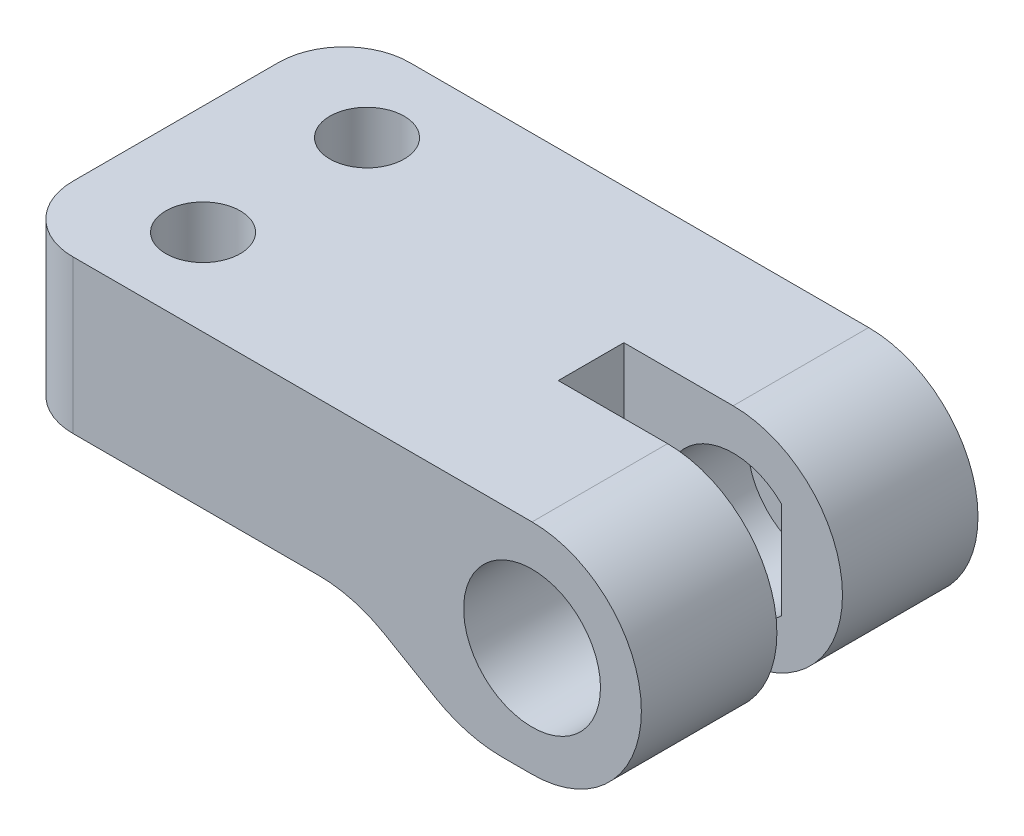
SolidWorks part; units mm, degrees
ref_plane "Płaszczyzna przednia" through (0, 0, 0) normal (0, 0, 1) x (1, 0, 0)
ref_plane "Płaszczyzna górna" through (0, 0, 0) normal (0, 1, 0) x (1, 0, 0)
ref_plane "Płaszczyzna prawa" through (0, 0, 0) normal (1, 0, 0) x (0, 0, -1)
sketch "Szkic1" plane through (0, 0, 0) normal (0, 0, 1) x (1, 0, 0)
  line L4 (0, 0) -> (-24, 0)
  line L5 (0, 0) -> (0, 10)
  line L6 (0, 10) -> (-24, 10)
  line L7 (-24, 0) -> (-24, 10)
  arc A0 (0, 10) -> (0, 0) centre (0, 5) cw
  dimension "D1" = 24
  dimension "D2" = 10
extrude "Dodanie-wyciągnięcie1" add sketch "Szkic1" along normal blind 15.4 contours A0 L5
sketch "Szkic2" plane through (0, 0, 15.4) normal (0, 0, 1) x (1, 0, 0)
  line L0 (0, 0) -> (-24, 0) construction
  circle A0 centre (0, 5) radius 3.13
  dimension "D1" = 5
  dimension "4" = 6.26
extrude "Wytnij-wyciągnięcie1" cut sketch "Szkic2" against normal blind 13
sketch "Szkic8" plane through (0, 4.76, 0) normal (0, 1, 0) x (1, 0, 0)
  circle A0 centre (-10, -9) radius 2
  dimension "D1" = 4
extrude "Wytnij-wyciągnięcie6" [suppressed] cut sketch "Szkic8" against normal through all
sketch "Szkic9" plane through (0, 0, 0) normal (0, 0, -1) x (-1, 0, 0)
  line L4 (24, 10) -> (0, 10)
  line L5 (0, 0) -> (24, 0)
  line L6 (24, 0) -> (24, 10)
  line L8 (24, 10) -> (0, 10)
  line L9 (0, 0) -> (24, 0)
  line L14 (24, 0) -> (24, 10)
  arc A5 (0, 10) -> (0, 0) centre (0, 5) ccw
  arc A8 (0, 10) -> (0, 0) centre (0, 5) ccw
  dimension "D1" = 0
sketch "Szkic10" plane through (0, 0, 17.88) normal (0, 0, 1) x (1, 0, 0)
  line L0 (2.2, 7.2264) -> (2.2, 2.7736)
  circle A0 centre (0, 5) radius 3.13 construction
  circle A2 centre (0, 5) radius 3.13
  arc A3 (2.2, 2.7736) -> (2.2, 7.2264) centre (0, 5) ccw
  dimension "D1" = 2.2
  dimension "D2" = 0
sketch "Szkic16" plane through (0, 0, 6.62) normal (0, 0, -1) x (-1, 0, 0)
  line L0 (31, 7) -> (16.1962, 7)
  line L1 (31, 10) -> (31, 0) construction
  line L2 (31, 3) -> (8.1531, 3)
  line L3 (31, 0) -> (0, 0) construction
  line L4 (27.25, 10) -> (23.75, 10) construction
  line L5 (16.1962, 7) -> (11, 10)
  line L7 (15.1, 10) -> (4.9, 10) construction
  line L8 (8.1531, 3) -> (3, 0)
  line L9 (31, 10) -> (31, 7)
  line L10 (31, 3) -> (31, 0)
  line L11 (31, 0) -> (3, 0)
  line L12 (11, 10) -> (31, 10)
  dimension "D1" = 3
  dimension "D2" = 3
  dimension "D3" = 30
  dimension "D4" = 20
  dimension "D5" = 28
extrude "Wytnij-wyciągnięcie13" cut sketch "Szkic16" against normal through all both and the other way through all
extrude "Dodanie-wyciągnięcie2" add sketch "Szkic10" along normal blind 13.5 from surface at -17.88 starting at face at (-9.0255, 4.3333, 0)
sketch "Szkic18" plane through (0, 10, 0) normal (0, 1, 0) x (1, 0, 0)
  line L0 (5, -15.4) -> (5, 0) construction
  line L1 (5, -9.2) -> (-5, -9.2)
  line L2 (5, -9.2) -> (5, -6.2)
  line L3 (5, -6.2) -> (-5, -6.2)
  line L4 (-5, -9.2) -> (-5, -6.2)
  line L5 (5, -6.2) -> (5, 0) construction
  line L6 (5, -9.2) -> (5, -15.4) construction
  dimension "D1" = 3
  dimension "D2" = 10
extrude "Wytnij-wyciągnięcie14" cut sketch "Szkic18" against normal through all
fillet "Zaokrąglenie2" radius 3 2 edges at (-24, 6.5, 0) (-24, 6.5, 15.4)
fillet "Zaokrąglenie3" radius 6 3 edges at (-3, 0, 12.3) (-3, 0, 3.1) (-8.1531, 3, 7.7)
sketch "Szkic19" plane through (0, 0, 9.2) normal (0, 0, -1) x (-1, 0, 0)
  line L4 (3.9862, 3) -> (13.9862, 3)
  line L6 (21, 3) -> (9.7724, 3) construction
  line L7 (14.1498, -4.9976) -> (-5.8502, -4.9976) construction
  line L8 (3.9862, 3) -> (0.7515, -7.1941)
  line L9 (0.7515, -7.1941) -> (13.9862, 3)
  dimension "D1" = 10
extrude "Wytnij-wyciągnięcie15" cut sketch "Szkic19" along normal blind 3
fillet "Zaokrąglenie5" radius 2 1 edges at (-5, 3, 7.7)
sketch "Szkic20" plane through (0, 10, 0) normal (0, 1, 0) x (1, 0, 0)
  line L0 (-19, -3.95) -> (-19, 0) construction
  line L1 (0, 0) -> (-21, 0) construction
  line L2 (-19, -11.45) -> (-19, -15.4) construction
  line L3 (0, -15.4) -> (-21, -15.4) construction
  line L4 (-19, -3.95) -> (-24, -3.95) construction
  line L5 (-24, -12.4) -> (-24, -3) construction
  line L6 (-19, -11.45) -> (-24, -11.45) construction
  line L7 (5, -6.2) -> (5, 0) construction
  circle A0 centre (-19, -3.95) radius 1.7
  circle A1 centre (-19, -11.45) radius 1.7
  dimension "D1" = 3.4
  dimension "D2" = 3.4
  dimension "D3" = 7.5
  dimension "D4" = 24
extrude "Wytnij-wyciągnięcie16" cut sketch "Szkic20" against normal through all
sketch "Szkic21" plane through (0, 3, 0) normal (0, -1, 0) x (-1, 0, 0)
  line L1 (15.7091, -3.95) -> (17.3546, -6.8)
  line L2 (17.3546, -6.8) -> (20.6454, -6.8)
  line L3 (20.6454, -6.8) -> (22.2909, -3.95)
  line L4 (22.2909, -3.95) -> (20.6454, -1.1)
  line L5 (20.6454, -1.1) -> (17.3546, -1.1)
  line L6 (17.3546, -1.1) -> (15.7091, -3.95)
  line L7 (15.7091, -11.45) -> (17.3546, -14.3)
  line L8 (17.3546, -14.3) -> (20.6454, -14.3)
  line L9 (20.6454, -14.3) -> (22.2909, -11.45)
  line L10 (22.2909, -11.45) -> (20.6454, -8.6)
  line L11 (20.6454, -8.6) -> (17.3546, -8.6)
  line L12 (17.3546, -8.6) -> (15.7091, -11.45)
  circle A0 centre (19, -3.95) radius 2.85 construction
  circle A1 centre (19, -11.45) radius 2.85 construction
  dimension "D1" = 5.7
  dimension "D2" = 5.7
extrude "Wytnij-wyciągnięcie17" cut sketch "Szkic21" against normal blind 3
